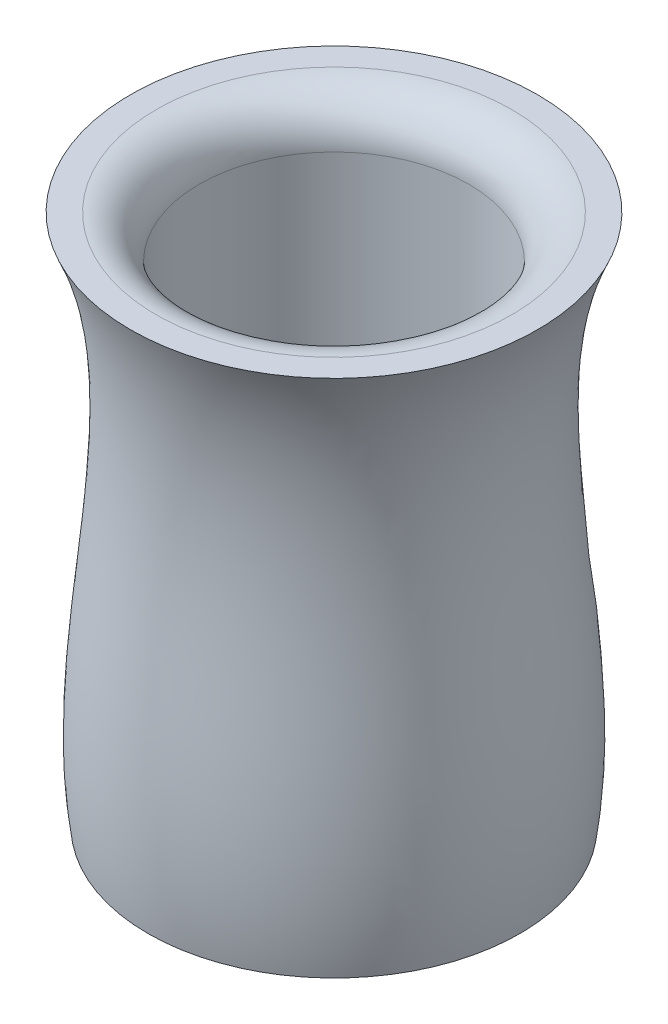
SolidWorks part; units mm, degrees
ref_plane "Front Plane" through (0, 0, 0) normal (0, 0, 1) x (1, 0, 0)
ref_plane "Top Plane" through (0, 0, 0) normal (0, 1, 0) x (1, 0, 0)
ref_plane "Right Plane" through (0, 0, 0) normal (1, 0, 0) x (0, 0, -1)
sketch "Sketch1" plane through (0, 0, 0) normal (0, 0, 1) x (1, 0, 0)
  line L0 (0, 86.7369) -> (0, -82.2576) construction
  line L1 (0, -41.9432) -> (43.1649, -41.9432)
  line L2 (47.237, 81.4431) -> (0, 81.4431)
  line L3 (0, -41.9432) -> (0, 81.4431)
  spline S0 degree 3 poles (43.1649, -41.9432) (49.2984, -1.239) (30.3819, 43.9022) (47.237, 81.4431) knots 0 0 0 0 1 1 1 1
revolve "Revolve1" add sketch "Sketch1" angle 360 about L0
sketch "Sketch2" plane through (0, 81.4431, 0) normal (0, 1, 0) x (1, 0, 0)
  circle A0 centre (0, 0) radius 31.2534
extrude "Cut-Extrude1" cut sketch "Sketch2" against normal blind 117
fillet "Fillet1" radius 10 1 edges at (0, 81.4431, 31.2534)
